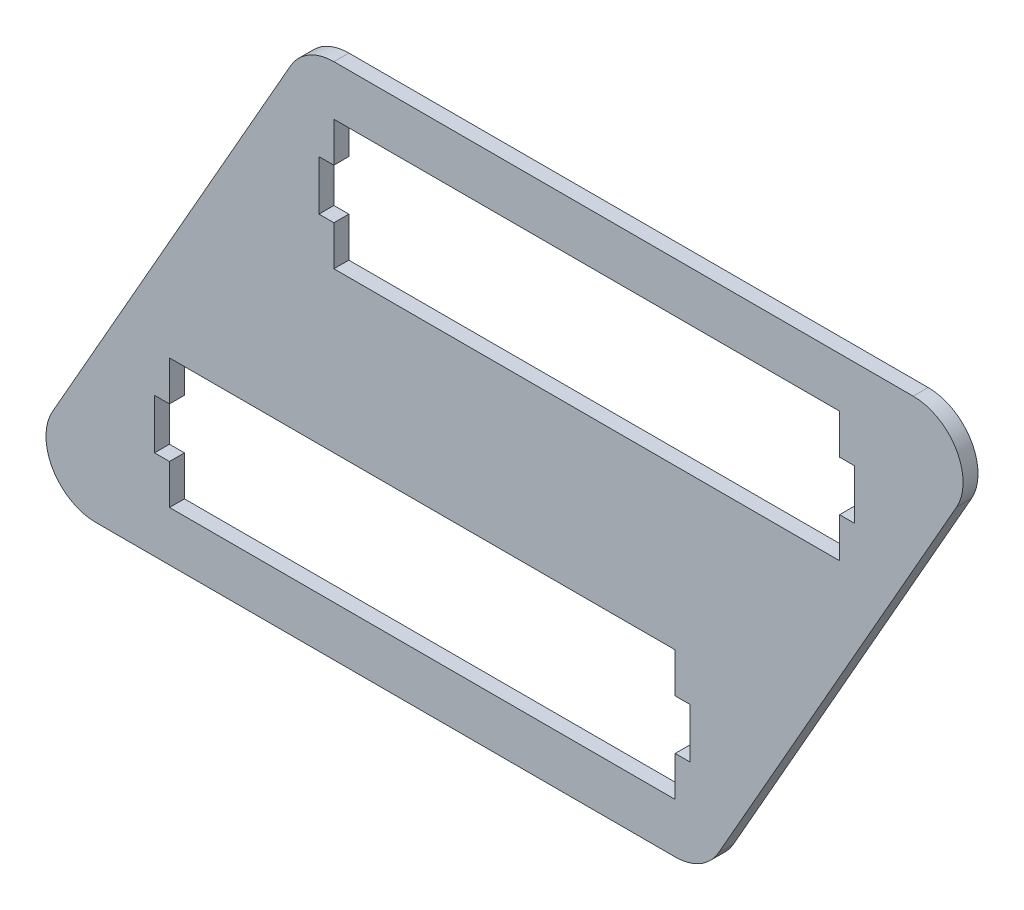
SolidWorks part; units mm, degrees
ref_plane "Ebene vorne" through (0, 0, 0) normal (0, 0, 1) x (1, 0, 0)
ref_plane "Ebene oben" through (0, 0, 0) normal (0, 1, 0) x (1, 0, 0)
ref_plane "Ebene rechts" through (0, 0, 0) normal (1, 0, 0) x (0, 0, -1)
sketch "Skizze1" plane through (0, 0, 0) normal (0, 0, 1) x (1, 0, 0)
  line L0 (0, 0) -> (59.1724, 104)
  line L1 (133.4881, 10) -> (31.9881, 10)
  line L2 (59.1724, 104) -> (198.4761, 104)
  line L3 (139.3037, 0) -> (198.4761, 104)
  line L4 (133.4881, 10) -> (133.4881, 36)
  line L5 (166.4881, 68) -> (64.9881, 68)
  line L6 (166.4881, 68) -> (166.4881, 94)
  line L7 (166.4881, 94) -> (64.9881, 94)
  line L8 (64.9881, 68) -> (64.9881, 94)
  line L9 (166.4881, 68) -> (64.9881, 94) construction
  line L10 (166.4881, 94) -> (64.9881, 68) construction
  line L11 (133.4881, 36) -> (31.9881, 36)
  line L12 (31.9881, 10) -> (31.9881, 36)
  line L13 (133.4881, 10) -> (31.9881, 36) construction
  line L14 (133.4881, 36) -> (31.9881, 10) construction
  line L15 (0, 0) -> (139.3037, 0)
  line L16 (168.8899, 52) -> (29.5862, 52) construction
  line L17 (115.7381, 81) -> (82.7381, 23) construction
  point P0 (115.7381, 81)
  point P10 (82.7381, 23)
  dimension "D1" = 101.5
  dimension "D2" = 26
  dimension "D3" = 101.5
  dimension "D4" = 26
  dimension "D5" = 32
  dimension "D6" = 33
  dimension "D8" = 10
  dimension "D7" = 10
extrude "Aufsatz-Linear austragen1" add sketch "Skizze1" along normal blind 3
fillet "Verrundung1" radius 10 4 edges at (0, 0, 1.5) (139.3037, 0, 1.5) (59.1724, 104, 1.5) (198.4761, 104, 1.5)
sketch "Skizze2" plane through (0, 0, 3) normal (0, 0, 1) x (1, 0, 0)
  line L0 (64.9881, 76) -> (61.9881, 76)
  line L1 (61.9881, 76) -> (61.9881, 86)
  line L2 (61.9881, 86) -> (64.9881, 86)
  line L3 (64.9881, 94) -> (64.9881, 68) construction
  line L4 (61.9881, 81) -> (64.9881, 81) construction
  line L5 (64.9881, 86) -> (64.9881, 76)
  line L6 (115.7381, 94) -> (115.7381, 68) construction
  line L7 (166.4881, 94) -> (64.9881, 94) construction
  line L8 (64.9881, 68) -> (166.4881, 68) construction
  line L9 (166.4881, 86) -> (166.4881, 76)
  line L10 (169.4881, 86) -> (166.4881, 86)
  line L11 (169.4881, 76) -> (169.4881, 86)
  line L12 (166.4881, 76) -> (169.4881, 76)
  line L13 (64.9881, 81) -> (31.9881, 23) construction
  line L14 (31.9881, 36) -> (31.9881, 10) construction
  line L15 (31.9881, 18) -> (28.9881, 18)
  line L16 (28.9881, 18) -> (28.9881, 28)
  line L17 (28.9881, 28) -> (31.9881, 28)
  line L18 (31.9881, 28) -> (31.9881, 18)
  line L19 (133.4881, 28) -> (133.4881, 18)
  line L20 (136.4881, 28) -> (133.4881, 28)
  line L21 (136.4881, 18) -> (136.4881, 28)
  line L22 (133.4881, 18) -> (136.4881, 18)
  line L23 (181.2812, 104) -> (64.9881, 104) construction
  line L24 (28.9881, 23) -> (31.9881, 23) construction
  dimension "D1" = 10
  dimension "D2" = 3
  dimension "D3" = 2
extrude "Schnitt-Linear austragen2" cut sketch "Skizze2" against normal up to next
equation "\"D7@Skizze1\"=\"D8@Skizze1\""
